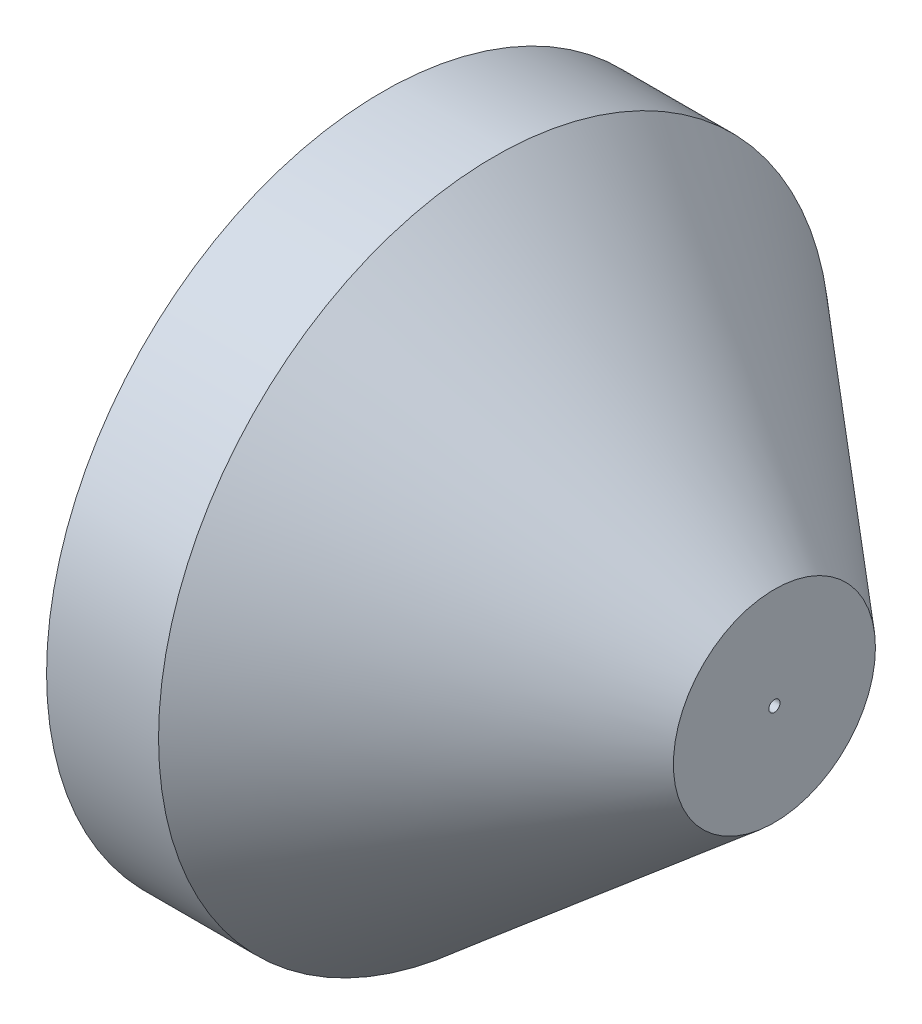
SolidWorks part; units mm, degrees
ref_plane "Front Plane" through (0, 0, 0) normal (0, 0, 1) x (1, 0, 0)
ref_plane "Top Plane" through (0, 0, 0) normal (0, 1, 0) x (1, 0, 0)
ref_plane "Right Plane" through (0, 0, 0) normal (1, 0, 0) x (0, 0, -1)
sketch "Sketch1" plane through (0, 0, 0) normal (1, 0, 0) x (0, 0, -1)
  circle A0 centre (0, 0) radius 30
  circle A1 centre (0, 0) radius 50
  dimension "D1" = 100
  dimension "D2" = 60
extrude "Boss-Extrude1" add sketch "Sketch1" along normal blind 20
sketch "Sketch2" plane through (20, 0, 0) normal (1, 0, 0) x (0, 0, -1)
  circle A3 centre (0, 0) radius 60
  dimension "D1" = 120
extrude "Boss-Extrude4" add sketch "Sketch2" along normal blind 50 draft 40
sketch "Sketch5" plane through (20, 0, 0) normal (-1, 0, 0) x (0, 0, 1)
  circle A0 centre (0, 0) radius 55
  circle A1 centre (0, 0) radius 60 construction
  circle A2 centre (0, 0) radius 60
  dimension "D1" = 110
extrude "Boss-Extrude5" add sketch "Sketch5" along normal blind 20
sketch "Sketch6" plane through (20, 0, 0) normal (-1, 0, 0) x (0, 0, 1)
  circle A0 centre (0, 0) radius 1
  dimension "D1" = 2
extrude "Cut-Extrude1" cut sketch "Sketch6" against normal through all
